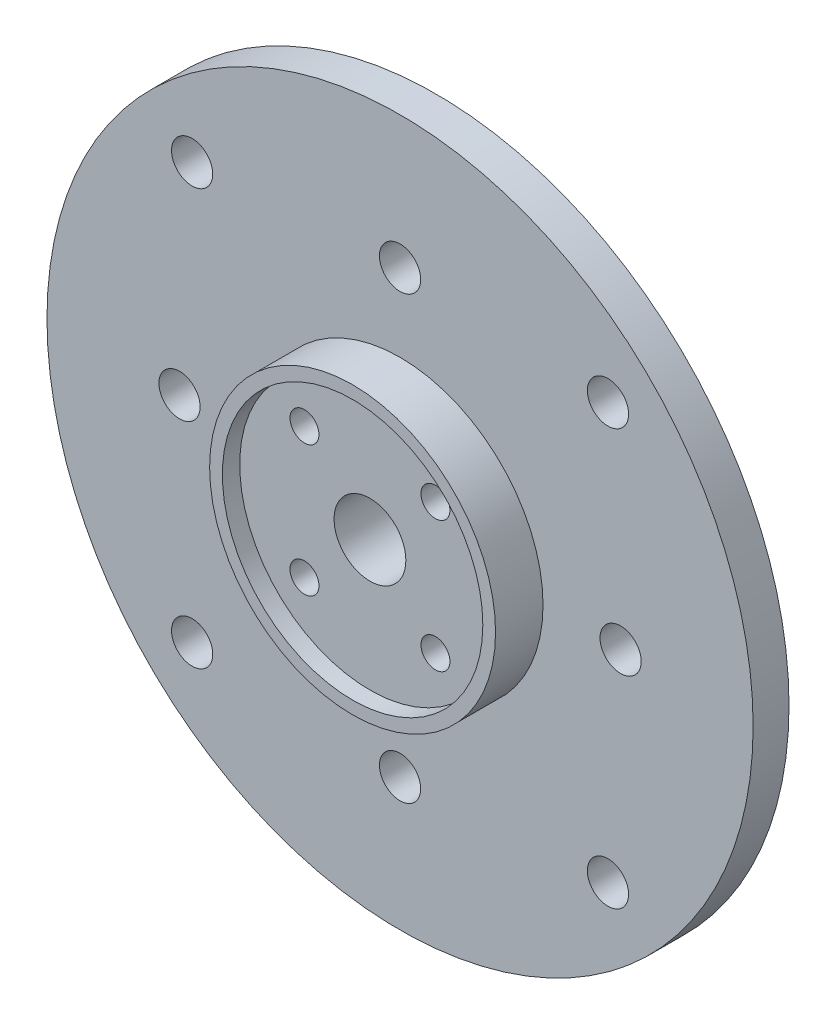
SolidWorks part; units mm, degrees
ref_plane "Front Plane" through (0, 0, 0) normal (0, 0, 1) x (1, 0, 0)
ref_plane "Top Plane" through (0, 0, 0) normal (0, 1, 0) x (1, 0, 0)
ref_plane "Right Plane" through (0, 0, 0) normal (1, 0, 0) x (0, 0, -1)
sketch "Sketch1" plane through (0, 0, 0) normal (0, 0, 1) x (1, 0, 0)
  line L0 (0, 30.5) -> (0, 0) construction
  line L1 (0, 0) -> (21.5668, 21.5668) construction
  circle A0 centre (0, 0) radius 30.5
  circle A1 centre (0, 19.05) radius 1.78
  circle A2 centre (19.05, 0) radius 1.78
  circle A3 centre (0, -19.05) radius 1.78
  circle A4 centre (-19.05, 0) radius 1.78
  circle A5 centre (17.9605, 17.9605) radius 1.78
  circle A6 centre (17.9605, -17.9605) radius 1.78
  circle A7 centre (-17.9605, -17.9605) radius 1.78
  circle A8 centre (-17.9605, 17.9605) radius 1.78
  point P15 (0, 0)
  point P25 (0, 0)
  dimension "D2" = 3.56
  dimension "D4" = 61
  dimension "D7" = 25.4
  dimension "D3" = 19.05
  dimension "D5" = 45
  dimension "D1" = 4
  dimension "D6" = 4
extrude "Boss-Extrude1" add sketch "Sketch1" along normal blind 3.1
sketch "Sketch2" plane through (0, 0, 3.1) normal (0, 0, 1) x (1, 0, 0)
  circle A0 centre (0, 0) radius 12.35
  dimension "D1" = 24.7
extrude "Boss-Extrude2" add sketch "Sketch2" along normal blind 4.1
sketch "Sketch3" plane through (0, 0, 7.2) normal (0, 0, 1) x (1, 0, 0)
  circle A0 centre (0, 0) radius 11.25
  dimension "D1" = 22.5
extrude "Cut-Extrude1" cut sketch "Sketch3" against normal blind 1.5
sketch "Sketch4" plane through (0, 0, 5.7) normal (0, 0, 1) x (1, 0, 0)
  line L0 (0, 11.25) -> (0, 0) construction
  line L1 (0, 0) -> (7.955, 7.955) construction
  circle A0 centre (0, 0) radius 11.25 construction
  circle A1 centre (0, 0) radius 11.25 construction
  circle A2 centre (5.6569, 5.6569) radius 1.25
  circle A3 centre (5.6569, -5.6569) radius 1.25
  circle A4 centre (-5.6569, -5.6569) radius 1.25
  circle A5 centre (-5.6569, 5.6569) radius 1.25
  circle A6 centre (0, 0) radius 3.1
  point P19 (0, 0)
  dimension "D4" = 2.5
  dimension "D5" = 6.2
  dimension "D1" = 45
  dimension "D3" = 8
  dimension "D2" = 4
extrude "Cut-Extrude2" cut sketch "Sketch4" against normal through all
